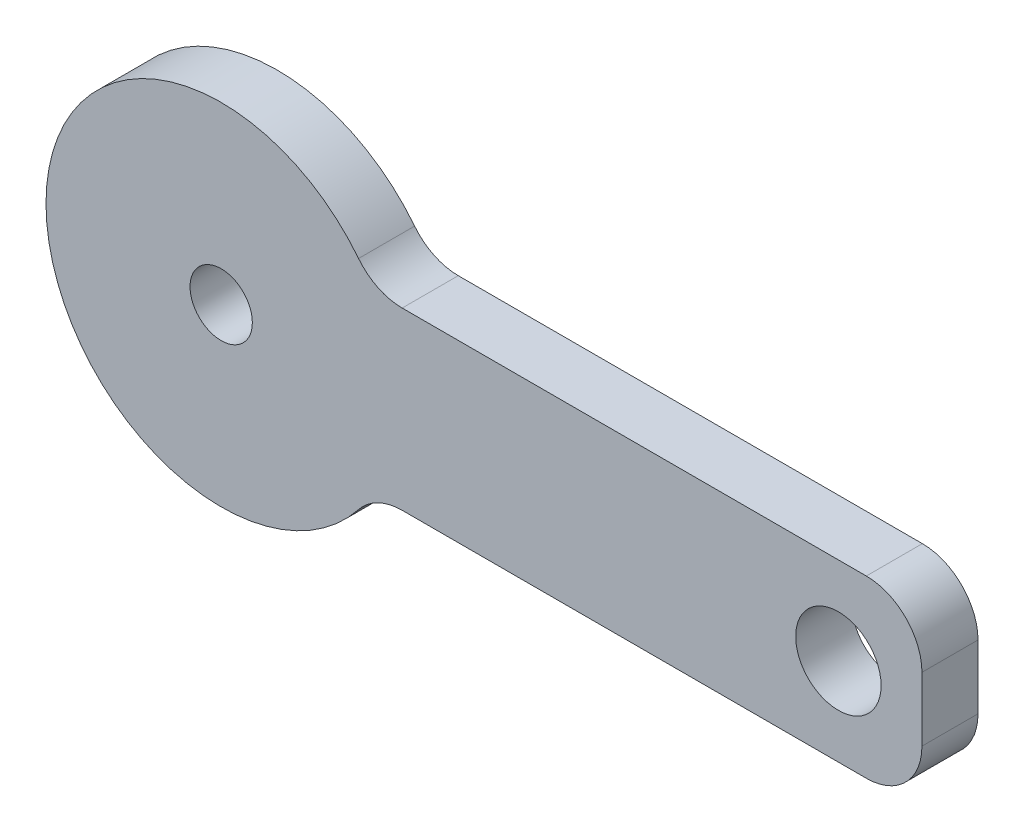
SolidWorks part; units mm, degrees
material "6061-T4 (SS)"
ref_plane "Front Plane" through (0, 0, 0) normal (0, 0, 1) x (1, 0, 0)
ref_plane "Top Plane" through (0, 0, 0) normal (0, 1, 0) x (1, 0, 0)
ref_plane "Right Plane" through (0, 0, 0) normal (1, 0, 0) x (0, 0, -1)
sketch "Sketch1" plane through (0, 0, 0) normal (0, 0, 1) x (1, 0, 0)
  line L1 (5.166, -2.5) -> (18.4125, -2.5)
  line L3 (5.166, 2.5) -> (18.4125, 2.5)
  line L4 (20, -0.9125) -> (20, 0.9125)
  arc A0 (3.9211, 3.1025) -> (3.9211, -3.1025) centre (0, 0) ccw
  arc A1 (5.166, -2.5) -> (3.9211, -3.1025) centre (5.166, -4.0875) ccw
  arc A2 (5.166, 2.5) -> (3.9211, 3.1025) centre (5.166, 4.0875) cw
  arc A3 (18.4125, 2.5) -> (20, 0.9125) centre (18.4125, 0.9125) cw
  arc A4 (18.4125, -2.5) -> (20, -0.9125) centre (18.4125, -0.9125) ccw
  point P12 (20, 2.5)
  point P15 (20, -2.5)
  dimension "D2" = 10
  dimension "D4" = 1.5875
  dimension "D5" = 1.5875
  dimension "D1" = 20
  dimension "D3" = 5
extrude "Boss-Extrude1" add sketch "Sketch1" along normal blind 1.6002
hole_wizard "#0 Clearance Hole1" positions "Sketch2" profile "Sketch3" hole size "#0" standard "ANSI Inch" end condition through all
sketch "Sketch2" plane through (0, 0, 1.6002) normal (0, 0, 1) x (1, 0, 0)
  point P0 (0, 0)
sketch "Sketch3" plane through (0, 0, 1.6002) normal (1, 0, 0) x (0, -1, 0)
  line L0 (0, 0) -> (0, 1.6002)
  line L1 (0, 1.6002) -> (0.889, 1.6002)
  line L2 (0.889, 1.6002) -> (0.889, 0)
  line L5 (0.889, 0) -> (0, 0)
  line L11 (0, -6.35) -> (0, 107.95) construction
  dimension "Thru Hole Dia." = 1.778
  dimension "Thru Hole Depth" = 1.6002
hole_wizard "#2 Clearance Hole1" positions "Sketch4" profile "Sketch5" hole size "#2" standard "ANSI Inch" end condition through all
sketch "Sketch4" plane through (0, 0, 1.6002) normal (0, 0, 1) x (1, 0, 0)
  line L5 (17.6156, 2.5) -> (17.6156, -2.5) construction
  line L6 (18.4125, 2.5) -> (5.166, 2.5) construction
  line L7 (5.166, -2.5) -> (18.4125, -2.5) construction
  point P0 (17.6156, 0)
sketch "Sketch5" plane through (17.6156, 0, 1.6002) normal (1, 0, 0) x (0, -1, 0)
  line L0 (0, 0) -> (0, 1.6002)
  line L1 (0, 1.6002) -> (1.2192, 1.6002)
  line L2 (1.2192, 1.6002) -> (1.2192, 0)
  line L5 (1.2192, 0) -> (0, 0)
  line L11 (0, -6.35) -> (0, 107.95) construction
  dimension "Thru Hole Dia." = 2.4384
  dimension "Thru Hole Depth" = 1.6002
